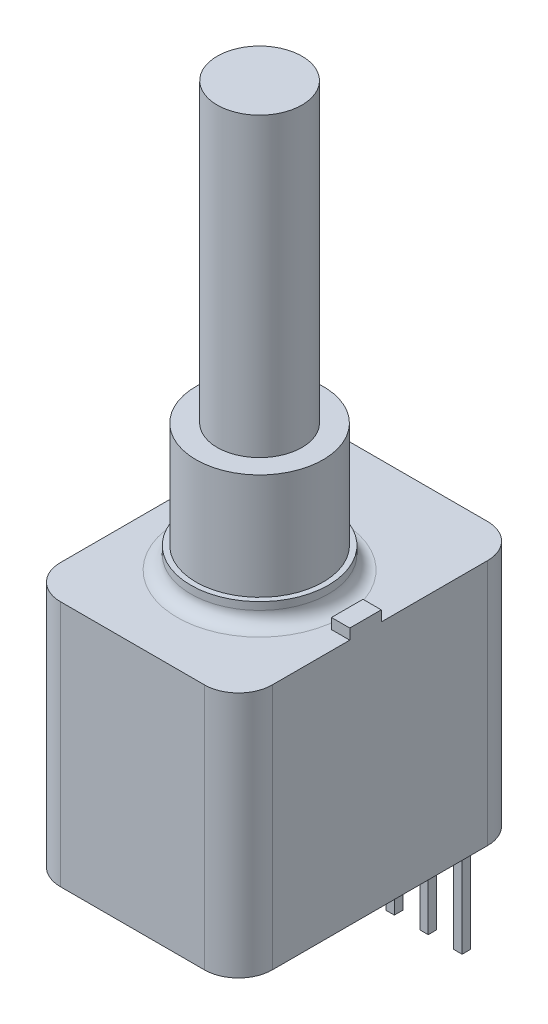
SolidWorks part; units mm, degrees
material "6061-T6 (SS)"
ref_plane "Front Plane" through (0, 0, 0) normal (0, 0, 1) x (1, 0, 0)
ref_plane "Top Plane" through (0, 0, 0) normal (0, 1, 0) x (1, 0, 0)
ref_plane "Right Plane" through (0, 0, 0) normal (1, 0, 0) x (0, 0, -1)
sketch "Sketch1" plane through (0, 0, 0) normal (0, 1, 0) x (1, 0, 0)
  line L0 (0, 1.08) -> (0, 0) construction
  line L1 (-7.9375, -9.525) -> (7.9375, -9.525)
  line L2 (-7.9375, -9.525) -> (-7.9375, 11.685)
  line L3 (-7.9375, 11.685) -> (7.9375, 11.685)
  line L4 (7.9375, -9.525) -> (7.9375, 11.685)
  line L5 (-7.9375, -9.525) -> (7.9375, 11.685) construction
  line L6 (-7.9375, 11.685) -> (7.9375, -9.525) construction
  dimension "D1" = 21.21
  dimension "D2" = 15.875
  dimension "D3" = 9.525
extrude "body" add sketch "Sketch1" along normal blind 18.5
sketch "Sketch2" plane through (0, 18.5, 0) normal (0, 1, 0) x (1, 0, 0)
  circle A0 centre (0, 0) radius 4.7625
  dimension "D1" = 9.525
extrude "3/8-32" add sketch "Sketch2" along normal blind 9.53
sketch "Sketch4" plane through (0, 28.03, 0) normal (0, 1, 0) x (1, 0, 0)
  circle A0 centre (0, 0) radius 3.175
  dimension "D1" = 6.35
extrude "shaft" add sketch "Sketch4" along normal blind 22.225
sketch "Sketch5" plane through (0, 18.5, 0) normal (0, 1, 0) x (1, 0, 0)
  circle A0 centre (0, 0) radius 5.1587
  dimension "D1" = 10.3175
extrude "boss" add sketch "Sketch5" along normal blind 1.5875
sketch "Sketch6" plane through (0, 18.5, 0) normal (0, 1, 0) x (1, 0, 0)
  line L0 (7.9375, -1.18) -> (7.9375, 1.18)
  line L1 (7.9375, -1.18) -> (6.5659, -1.18)
  line L2 (7.9375, 1.18) -> (6.5659, 1.18)
  line L3 (6.5659, -1.18) -> (6.5659, 1.18)
  line L6 (6.5659, 0) -> (0, 0) construction
  line L7 (7.9375, -9.525) -> (7.9375, 11.685) construction
  point P0 (-7.9375, 0)
  dimension "D1" = 2.36
  dimension "D2" = 1.3716
extrude "anti-rotation lug" add sketch "Sketch6" along normal blind 0.7874
sketch "Sketch7" plane through (0, 0, 0) normal (0, -1, 0) x (1, 0, 0)
  line L0 (0, -11.685) -> (0, 9.525) construction
  line L1 (7.9375, -11.685) -> (-7.9375, -11.685) construction
  line L2 (-2.8575, -9.78) -> (-2.2225, -10.415) construction
  line L3 (-5.3975, -9.78) -> (-4.7625, -9.78)
  line L4 (-5.3975, -9.78) -> (-5.3975, -10.415)
  line L5 (-5.3975, -10.415) -> (-4.7625, -10.415)
  line L6 (-4.7625, -9.78) -> (-4.7625, -10.415)
  line L7 (-5.3975, -9.78) -> (-4.7625, -10.415) construction
  line L8 (-5.3975, -10.415) -> (-4.7625, -9.78) construction
  line L9 (-2.8575, -10.415) -> (-2.2225, -9.78) construction
  line L10 (-2.8575, -9.78) -> (-2.8575, -10.415)
  line L11 (-2.8575, -9.78) -> (-2.2225, -9.78)
  line L12 (-2.2225, -9.78) -> (-2.2225, -10.415)
  line L13 (-2.8575, -10.415) -> (-2.2225, -10.415)
  line L14 (-0.3175, -9.78) -> (0.3175, -10.415) construction
  line L15 (-0.3175, -10.415) -> (0.3175, -9.78) construction
  line L16 (-0.3175, -9.78) -> (-0.3175, -10.415)
  line L17 (-0.3175, -9.78) -> (0.3175, -9.78)
  line L18 (0.3175, -9.78) -> (0.3175, -10.415)
  line L19 (-0.3175, -10.415) -> (0.3175, -10.415)
  line L20 (2.2225, -9.78) -> (2.8575, -10.415) construction
  line L21 (2.2225, -10.415) -> (2.8575, -9.78) construction
  line L22 (2.2225, -9.78) -> (2.2225, -10.415)
  line L23 (2.2225, -9.78) -> (2.8575, -9.78)
  line L24 (2.8575, -9.78) -> (2.8575, -10.415)
  line L25 (2.2225, -10.415) -> (2.8575, -10.415)
  line L26 (4.7625, -9.78) -> (5.3975, -10.415) construction
  line L27 (4.7625, -10.415) -> (5.3975, -9.78) construction
  line L28 (4.7625, -9.78) -> (4.7625, -10.415)
  line L29 (4.7625, -9.78) -> (5.3975, -9.78)
  line L30 (5.3975, -9.78) -> (5.3975, -10.415)
  line L31 (4.7625, -10.415) -> (5.3975, -10.415)
  line L32 (-5.08, -10.0975) -> (-2.54, -10.0975) construction
  line L34 (-7.9375, 9.525) -> (7.9375, 9.525) construction
  point P5 (-5.08, -10.0975)
  point P10 (-2.54, -10.0975)
  point P16 (0, -10.0975)
  point P21 (2.54, -10.0975)
  point P26 (5.08, -10.0975)
  dimension "D2" = 2.54
  dimension "D3" = 0.635
  dimension "D4" = 1.5875
  dimension "D1" = 5
extrude "pins" add sketch "Sketch7" along normal blind 8.636
fillet "Fillet1" radius 1.016 1 edges at (0, 18.5, -5.1587)
fillet "Fillet2" radius 2.54 4 edges at (7.9375, 9.25, 9.525) (-7.9375, 9.25, 9.525) (-7.9375, 9.25, -11.685) (7.9375, 9.25, -11.685)
